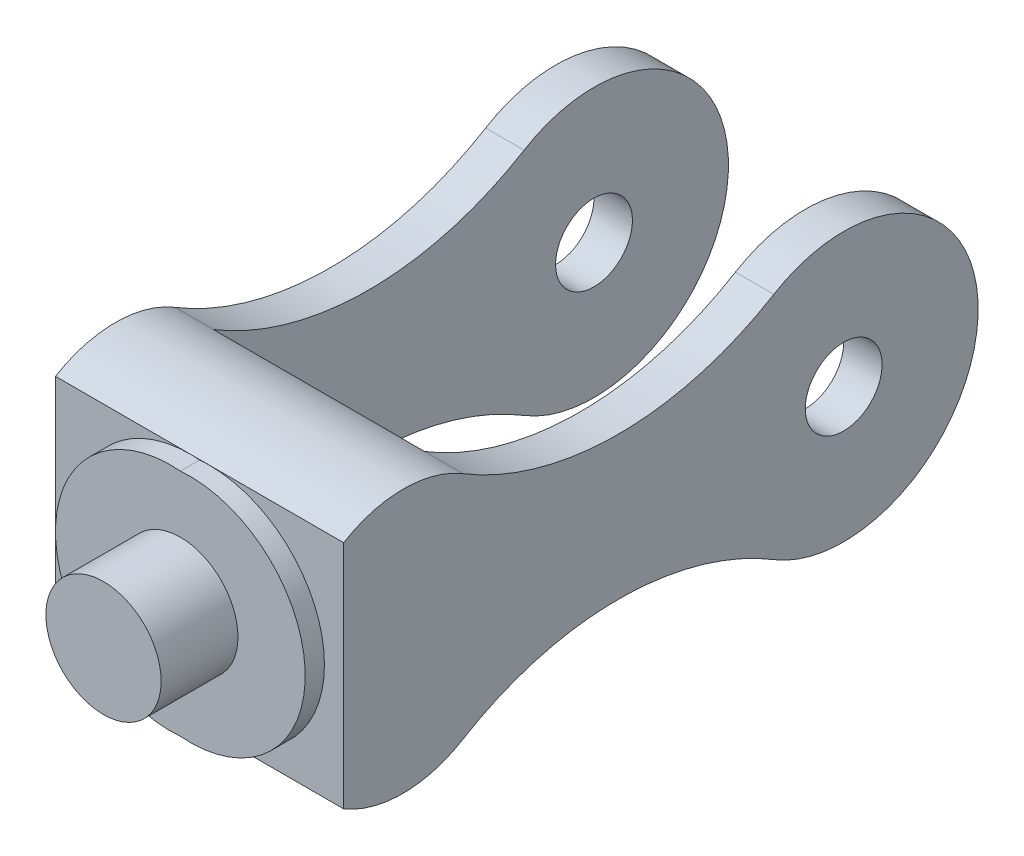
SolidWorks part; units mm, degrees
ref_plane "Front Plane" through (0, 0, 0) normal (0, 0, 1) x (1, 0, 0)
ref_plane "Top Plane" through (0, 0, 0) normal (0, 1, 0) x (1, 0, 0)
ref_plane "Right Plane" through (0, 0, 0) normal (1, 0, 0) x (0, 0, -1)
sketch "Sketch1" plane through (0, 0, 0) normal (0, 0, 1) x (1, 0, 0)
  circle A0 centre (0, 0) radius 30
  dimension "D1" = 60
extrude "Boss-Extrude1" add sketch "Sketch1" along normal blind 5
ref_plane "Plane1" through (30, 0, 0) normal (1, 0, 0) x (0, 0, -1)
sketch "Sketch2" plane through (30, 0, 0) normal (1, 0, 0) x (0, 0, -1)
  line L0 (0, 30) -> (0, -30)
  arc A0 (0, 30) -> (31.1034, 30) centre (15.5517, 4.3457) cw
  arc A1 (31.1034, 30) -> (111.9722, 30) centre (71.5378, 96.7013) ccw
  arc A2 (31.1034, -29.8066) -> (111.9722, -29.8066) centre (71.5378, -96.5079) cw
  arc A3 (0, -30) -> (31.1034, -29.8066) centre (15.3922, -4.2497) ccw
  arc A4 (111.9722, -29.8066) -> (111.9722, 30) centre (130.1599, 0.0967) ccw
  dimension "D2" = 30
  dimension "D3" = 78
  dimension "D4" = 70
extrude "Boss-Extrude2" add sketch "Sketch2" along normal blind 10 separate body
sketch "Sketch3" plane through (30, 0, 0) normal (-1, 0, 0) x (0, 0, 1)
  line L0 (-31.1034, 30) -> (-31.1034, -29.8066)
  line L1 (0, -30) -> (0, 30)
  line L2 (0, -30) -> (0, 30)
  arc A5 (0, 30) -> (-31.1034, 30) centre (-15.5517, 4.3457) ccw
  arc A6 (-111.9722, 30) -> (-31.1034, 30) centre (-71.5378, 96.7013) ccw
  arc A7 (-111.9722, 30) -> (-111.9722, -29.8066) centre (-130.1599, 0.0967) ccw
  arc A8 (-31.1034, -29.8066) -> (-111.9722, -29.8066) centre (-71.5378, -96.5079) ccw
  arc A9 (-31.1034, -29.8066) -> (0, -30) centre (-15.3922, -4.2497) ccw
  arc A10 (0, 30) -> (-31.1034, 30) centre (-15.5517, 4.3457) ccw
  arc A14 (-31.1034, -29.8066) -> (0, -30) centre (-15.3922, -4.2497) ccw
  dimension "D1" = 0
extrude "Boss-Extrude3" add sketch "Sketch3" along normal blind 55
ref_plane "Plane2" through (2.5, 0, 0) normal (-1, 0, 0) x (0, 0, 1)
mirror "Mirror1" about plane through (2.5, 0, 0) normal (-1, 0, 0) of bodies 105
sketch "Sketch4" plane through (0, 0, 5) normal (0, 0, 1) x (1, 0, 0)
  line L0 (2.5, -30) -> (2.5, 30) construction
  line L1 (0, -30) -> (5, -30) construction
  line L2 (0, 30) -> (5, 30) construction
  circle A0 centre (2.5, 0) radius 15
  dimension "D1" = 30
extrude "Boss-Extrude4" add sketch "Sketch4" along normal blind 20
sketch "Sketch5" plane through (30, 0, 0) normal (-1, 0, 0) x (0, 0, 1)
  circle A0 centre (-130.1599, 0.0967) radius 10
  dimension "D1" = 20
extrude "Cut-Extrude1" cut sketch "Sketch5" against normal blind 10
mirror "Mirror2" about plane through (2.5, 0, 0) normal (-1, 0, 0) of "Cut-Extrude1"
